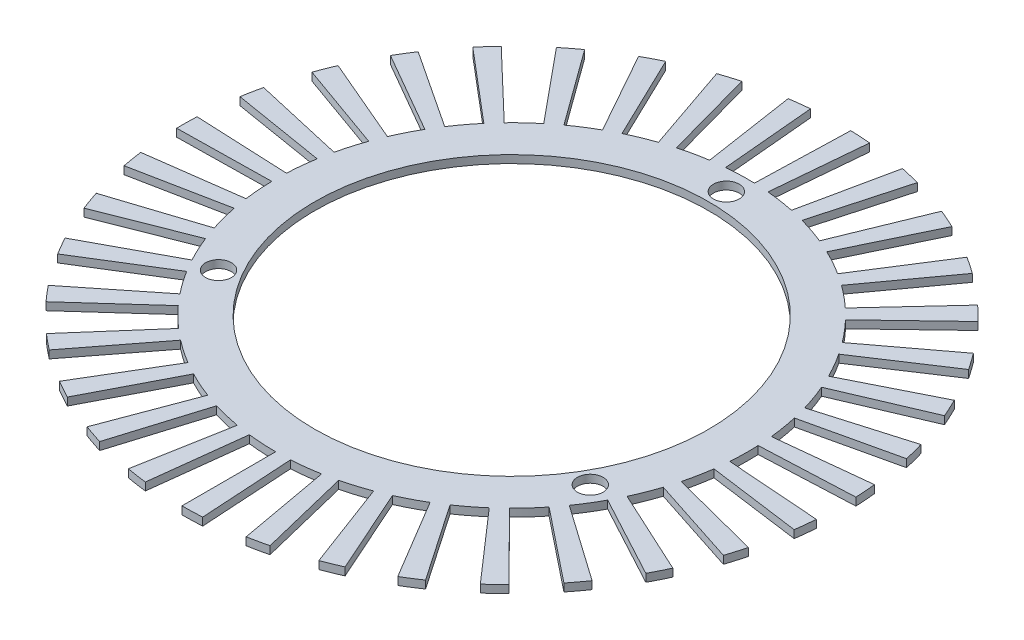
SolidWorks part; units mm, degrees
material "AISI 1010 Steel, hot rolled bar"
ref_plane "Front Plane" through (0, 0, 0) normal (0, 0, 1) x (1, 0, 0)
ref_plane "Top Plane" through (0, 0, 0) normal (0, 1, 0) x (1, 0, 0)
ref_plane "Right Plane" through (0, 0, 0) normal (1, 0, 0) x (0, 0, -1)
sketch "Sketch1" plane through (0, 0, 0) normal (0, 1, 0) x (1, 0, 0)
  circle A0 centre (0, 0) radius 25.25
  dimension "D1" = 50.5
extrude "Extrude-Thin1" add sketch "Sketch1" against normal blind 1 thin
sketch "Sketch2" plane through (0, 0, 0) normal (0, 1, 0) x (1, 0, 0)
  line L0 (0, -30.25) -> (0, 30.25) construction
  line L1 (0, 0) -> (23.8157, -13.75) construction
  line L2 (0, 0) -> (-23.8157, -13.75) construction
  circle A0 centre (0, 27.5) radius 1.65
  circle A1 centre (0, 0) radius 30.25 construction
  circle A4 centre (0, 0) radius 27.5 construction
  circle A7 centre (23.8157, -13.75) radius 1.65
  circle A8 centre (-23.8157, -13.75) radius 1.65
  dimension "D1" = 55
  dimension "D2" = 3.3
  dimension "D3" = 120
  dimension "D4" = 120
extrude "Cut-Extrude3" cut sketch "Sketch2" against normal blind 10
sketch "Sketch5" plane through (0, -1, 0) normal (0, -1, 0) x (1, 0, 0)
  line L0 (0, 0) -> (0, 35.9971) construction
  line L1 (0, 0) -> (2.0822, 34.0432) construction
  line L2 (0, 42.25) -> (0, 30.25)
  line L3 (1.8467, 30.1936) -> (2.5793, 42.1712)
  line L4 (7.544, 41.571) -> (5.4013, 29.7639)
  line L5 (7.2083, 29.3786) -> (10.0678, 41.0329)
  line L6 (14.8456, 39.5559) -> (10.6291, 28.3211)
  line L7 (12.3382, 27.6194) -> (17.2327, 38.5758)
  line L8 (21.67, 36.2695) -> (15.5152, 25.9681)
  line L9 (17.0716, 24.9725) -> (23.8438, 34.8789)
  line L10 (27.7979, 31.8173) -> (19.9026, 22.7804)
  line L11 (21.2562, 21.5229) -> (29.6885, 30.0609)
  line L12 (33.0324, 26.3424) -> (23.6504, 18.8606)
  line L13 (24.7577, 17.3816) -> (34.5789, 24.2767)
  line L14 (37.2052, 20.021) -> (26.638, 14.3345)
  line L15 (27.4634, 12.6816) -> (38.358, 17.7123)
  line L16 (40.1821, 13.056) -> (28.7695, 9.3478)
  line L17 (29.2865, 7.574) -> (40.9042, 10.5786)
  line L18 (41.8676, 5.6714) -> (29.9762, 4.0606)
  line L19 (30.1682, 2.223) -> (42.1358, 3.1048)
  line L20 (42.2075, -1.8955) -> (30.2195, -1.3572)
  line L21 (30.0803, -3.1995) -> (42.013, -4.4687)
  line L48 (41.1907, -9.4015) -> (29.4916, -6.7313)
  line L49 (29.0256, -8.5191) -> (40.5399, -11.8986)
  line L50 (38.85, -16.6053) -> (27.8157, -11.889)
  line L51 (27.038, -13.5649) -> (37.7639, -18.9461)
  line L52 (35.2607, -23.2754) -> (25.2458, -16.6646)
  line L53 (24.1814, -18.1748) -> (33.774, -25.3846)
  line L54 (30.5381, -29.1974) -> (21.8645, -20.9046)
  line L55 (20.5476, -22.2005) -> (28.6987, -31.0072)
  line L56 (24.8339, -34.181) -> (17.7805, -24.4728)
  line L57 (16.2533, -25.5126) -> (22.7009, -35.6333)
  line L58 (18.3316, -38.0659) -> (13.125, -27.2543)
  line L59 (11.4367, -28.0047) -> (15.9735, -39.1141)
  line L60 (11.2401, -40.7274) -> (8.0476, -29.1599)
  line L61 (6.2524, -29.5968) -> (8.7327, -41.3377)
  line L62 (3.7873, -42.0799) -> (2.7116, -30.1282)
  line L63 (0.8672, -30.2376) -> (1.2113, -42.2326)
  line L64 (-3.7873, -42.0799) -> (-2.7116, -30.1282)
  line L65 (-4.5458, -29.9065) -> (-6.3491, -41.7702)
  line L66 (-11.2401, -40.7274) -> (-8.0476, -29.1599)
  line L67 (-9.8128, -28.6142) -> (-13.7054, -39.9653)
  line L68 (-18.3316, -38.0659) -> (-13.125, -27.2543)
  line L69 (-14.7643, -26.4022) -> (-20.6213, -36.8758)
  line L70 (-24.8339, -34.181) -> (-17.7805, -24.4728)
  line L71 (-19.2414, -23.3416) -> (-26.8743, -32.6011)
  line L72 (-30.5381, -29.1974) -> (-21.8645, -20.9046)
  line L73 (-23.1, -19.5309) -> (-32.2636, -27.2786)
  line L74 (-35.2607, -23.2754) -> (-25.2458, -16.6646)
  line L75 (-26.2161, -15.0923) -> (-36.6159, -21.0794)
  line L76 (-38.85, -16.6053) -> (-27.8157, -11.889)
  line L77 (-28.4896, -10.1687) -> (-39.7913, -14.2026)
  line L78 (-41.1907, -9.4015) -> (-29.4916, -6.7313)
  line L79 (-29.8475, -4.9183) -> (-41.6878, -6.8693)
  line L80 (-42.2075, -1.8955) -> (-30.2195, -1.3572)
  line L81 (-30.246, 0.4902) -> (-42.2445, 0.6847)
  line L82 (-41.8676, 5.6714) -> (-29.9762, 4.0606)
  line L83 (-29.6724, 5.883) -> (-41.4433, 8.2167)
  line L84 (-40.1821, 13.056) -> (-28.7695, 9.3478)
  line L85 (-28.1451, 11.0867) -> (-39.3101, 15.4847)
  line L86 (-37.2052, 20.021) -> (-26.638, 14.3345)
  line L87 (-25.7132, 15.934) -> (-35.9135, 22.2549)
  line L88 (-33.0324, 26.3424) -> (-23.6504, 18.8606)
  line L89 (-22.4549, 20.2692) -> (-31.3626, 28.3099)
  line L90 (-27.7979, 31.8173) -> (-19.9026, 22.7804)
  line L91 (-18.4748, 23.9529) -> (-25.8037, 33.4549)
  line L92 (-21.67, 36.2695) -> (-15.5152, 25.9681)
  line L93 (-13.901, 26.8668) -> (-19.4154, 37.5247)
  line L94 (-14.8456, 39.5559) -> (-10.6291, 28.3211)
  line L95 (-8.8803, 28.9172) -> (-12.4031, 40.3884)
  line L96 (-7.544, 41.571) -> (-5.4013, 29.7639)
  line L97 (-3.5742, 30.0381) -> (-4.9921, 41.954)
  circle A0 centre (0, 0) radius 30.25 construction
  arc A1 (1.8467, 30.1936) -> (0, 30.25) centre (0, 0) ccw
  arc A2 (2.5793, 42.1712) -> (0, 42.25) centre (0, 0) ccw
  arc A3 (10.0678, 41.0329) -> (7.544, 41.571) centre (0, 0) ccw
  arc A4 (7.2083, 29.3786) -> (5.4013, 29.7639) centre (0, 0) ccw
  arc A5 (17.2327, 38.5758) -> (14.8456, 39.5559) centre (0, 0) ccw
  arc A6 (12.3382, 27.6194) -> (10.6291, 28.3211) centre (0, 0) ccw
  arc A7 (23.8438, 34.8789) -> (21.67, 36.2695) centre (0, 0) ccw
  arc A8 (17.0716, 24.9725) -> (15.5152, 25.9681) centre (0, 0) ccw
  arc A9 (29.6885, 30.0609) -> (27.7979, 31.8173) centre (0, 0) ccw
  arc A10 (21.2562, 21.5229) -> (19.9026, 22.7804) centre (0, 0) ccw
  arc A11 (34.5789, 24.2767) -> (33.0324, 26.3424) centre (0, 0) ccw
  arc A12 (24.7577, 17.3816) -> (23.6504, 18.8606) centre (0, 0) ccw
  arc A13 (38.358, 17.7123) -> (37.2052, 20.021) centre (0, 0) ccw
  arc A14 (27.4634, 12.6816) -> (26.638, 14.3345) centre (0, 0) ccw
  arc A15 (40.9042, 10.5786) -> (40.1821, 13.056) centre (0, 0) ccw
  arc A16 (29.2865, 7.574) -> (28.7695, 9.3478) centre (0, 0) ccw
  arc A17 (42.1358, 3.1048) -> (41.8676, 5.6714) centre (0, 0) ccw
  arc A18 (30.1682, 2.223) -> (29.9762, 4.0606) centre (0, 0) ccw
  arc A19 (42.013, -4.4687) -> (42.2075, -1.8955) centre (0, 0) ccw
  arc A20 (30.0803, -3.1995) -> (30.2195, -1.3572) centre (0, 0) ccw
  arc A47 (40.5399, -11.8986) -> (41.1907, -9.4015) centre (0, 0) ccw
  arc A48 (29.0256, -8.5191) -> (29.4916, -6.7313) centre (0, 0) ccw
  arc A49 (37.7639, -18.9461) -> (38.85, -16.6053) centre (0, 0) ccw
  arc A50 (27.038, -13.5649) -> (27.8157, -11.889) centre (0, 0) ccw
  arc A51 (33.774, -25.3846) -> (35.2607, -23.2754) centre (0, 0) ccw
  arc A52 (24.1814, -18.1748) -> (25.2458, -16.6646) centre (0, 0) ccw
  arc A53 (28.6987, -31.0072) -> (30.5381, -29.1974) centre (0, 0) ccw
  arc A54 (20.5476, -22.2005) -> (21.8645, -20.9046) centre (0, 0) ccw
  arc A55 (22.7009, -35.6333) -> (24.8339, -34.181) centre (0, 0) ccw
  arc A56 (16.2533, -25.5126) -> (17.7805, -24.4728) centre (0, 0) ccw
  arc A57 (15.9735, -39.1141) -> (18.3316, -38.0659) centre (0, 0) ccw
  arc A58 (11.4367, -28.0047) -> (13.125, -27.2543) centre (0, 0) ccw
  arc A59 (8.7327, -41.3377) -> (11.2401, -40.7274) centre (0, 0) ccw
  arc A60 (6.2524, -29.5968) -> (8.0476, -29.1599) centre (0, 0) ccw
  arc A61 (1.2113, -42.2326) -> (3.7873, -42.0799) centre (0, 0) ccw
  arc A62 (0.8672, -30.2376) -> (2.7116, -30.1282) centre (0, 0) ccw
  arc A63 (-6.3491, -41.7702) -> (-3.7873, -42.0799) centre (0, 0) ccw
  arc A64 (-4.5458, -29.9065) -> (-2.7116, -30.1282) centre (0, 0) ccw
  arc A65 (-13.7054, -39.9653) -> (-11.2401, -40.7274) centre (0, 0) ccw
  arc A66 (-9.8128, -28.6142) -> (-8.0476, -29.1599) centre (0, 0) ccw
  arc A67 (-20.6213, -36.8758) -> (-18.3316, -38.0659) centre (0, 0) ccw
  arc A68 (-14.7643, -26.4022) -> (-13.125, -27.2543) centre (0, 0) ccw
  arc A69 (-26.8743, -32.6011) -> (-24.8339, -34.181) centre (0, 0) ccw
  arc A70 (-19.2414, -23.3416) -> (-17.7805, -24.4728) centre (0, 0) ccw
  arc A71 (-32.2636, -27.2786) -> (-30.5381, -29.1974) centre (0, 0) ccw
  arc A72 (-23.1, -19.5309) -> (-21.8645, -20.9046) centre (0, 0) ccw
  arc A73 (-36.6159, -21.0794) -> (-35.2607, -23.2754) centre (0, 0) ccw
  arc A74 (-26.2161, -15.0923) -> (-25.2458, -16.6646) centre (0, 0) ccw
  arc A75 (-39.7913, -14.2026) -> (-38.85, -16.6053) centre (0, 0) ccw
  arc A76 (-28.4896, -10.1687) -> (-27.8157, -11.889) centre (0, 0) ccw
  arc A77 (-41.6878, -6.8693) -> (-41.1907, -9.4015) centre (0, 0) ccw
  arc A78 (-29.8475, -4.9183) -> (-29.4916, -6.7313) centre (0, 0) ccw
  arc A79 (-42.2445, 0.6847) -> (-42.2075, -1.8955) centre (0, 0) ccw
  arc A80 (-30.246, 0.4902) -> (-30.2195, -1.3572) centre (0, 0) ccw
  arc A81 (-41.4433, 8.2167) -> (-41.8676, 5.6714) centre (0, 0) ccw
  arc A82 (-29.6724, 5.883) -> (-29.9762, 4.0606) centre (0, 0) ccw
  arc A83 (-39.3101, 15.4847) -> (-40.1821, 13.056) centre (0, 0) ccw
  arc A84 (-28.1451, 11.0867) -> (-28.7695, 9.3478) centre (0, 0) ccw
  arc A85 (-35.9135, 22.2549) -> (-37.2052, 20.021) centre (0, 0) ccw
  arc A86 (-25.7132, 15.934) -> (-26.638, 14.3345) centre (0, 0) ccw
  arc A87 (-31.3626, 28.3099) -> (-33.0324, 26.3424) centre (0, 0) ccw
  arc A88 (-22.4549, 20.2692) -> (-23.6504, 18.8606) centre (0, 0) ccw
  arc A89 (-25.8037, 33.4549) -> (-27.7979, 31.8173) centre (0, 0) ccw
  arc A90 (-18.4748, 23.9529) -> (-19.9026, 22.7804) centre (0, 0) ccw
  arc A91 (-19.4154, 37.5247) -> (-21.67, 36.2695) centre (0, 0) ccw
  arc A92 (-13.901, 26.8668) -> (-15.5152, 25.9681) centre (0, 0) ccw
  arc A93 (-12.4031, 40.3884) -> (-14.8456, 39.5559) centre (0, 0) ccw
  arc A94 (-8.8803, 28.9172) -> (-10.6291, 28.3211) centre (0, 0) ccw
  arc A95 (-4.9921, 41.954) -> (-7.544, 41.571) centre (0, 0) ccw
  arc A96 (-3.5742, 30.0381) -> (-5.4013, 29.7639) centre (0, 0) ccw
  point P87 (0, 0)
  dimension "D2" = 12
  dimension "D1" = 3.5
  dimension "D3" = 35
extrude "Boss-Extrude1" add sketch "Sketch5" against normal blind 1
